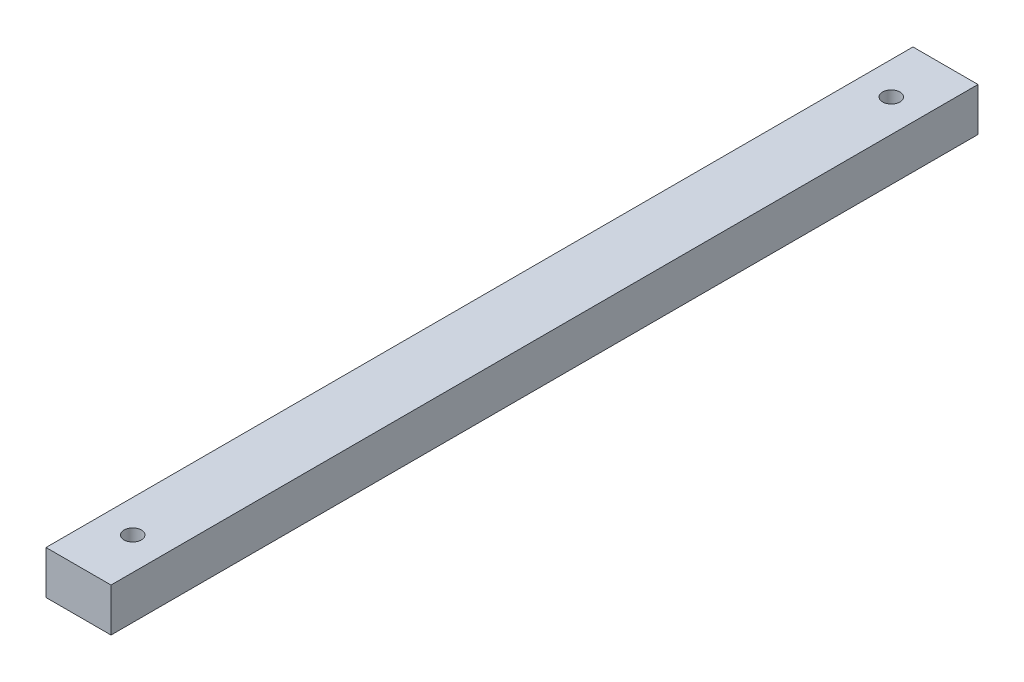
SolidWorks part; units mm, degrees
material "Roble"
ref_plane "Alzado" through (0, 0, 0) normal (0, 0, 1) x (1, 0, 0)
ref_plane "Planta" through (0, 0, 0) normal (0, 1, 0) x (1, 0, 0)
ref_plane "Vista lateral" through (0, 0, 0) normal (1, 0, 0) x (0, 0, -1)
sketch "Croquis1" plane through (0, 0, 0) normal (0, 0, 1) x (1, 0, 0)
  line L1 (15, 10) -> (-15, 10)
  line L2 (15, 10) -> (15, -10)
  line L3 (15, -10) -> (-15, -10)
  line L4 (-15, 10) -> (-15, -10)
  line L5 (15, 10) -> (-15, -10) construction
  line L6 (15, -10) -> (-15, 10) construction
  point P0 (0, 0)
  dimension "D1" = 30
  dimension "D2" = 20
extrude "Saliente-Extruir1" add sketch "Croquis1" along normal blind 400
sketch "Croquis2" plane through (0, 10, 0) normal (0, 1, 0) x (1, 0, 0)
  line L0 (-15, -200) -> (46.7331, -200) construction
  line L1 (-15, -400) -> (-15, 0) construction
  line L2 (0, -400) -> (0, 0) construction
  line L3 (15, -400) -> (-15, -400) construction
  line L4 (15, 0) -> (-15, 0) construction
  circle A0 centre (0, -375) radius 4
  circle A1 centre (0, -25) radius 4
  dimension "D3" = 8
  dimension "D4" = 8
  dimension "D1" = 175
  dimension "D2" = 175
extrude "Cortar-Extruir1" cut sketch "Croquis2" against normal blind 400
